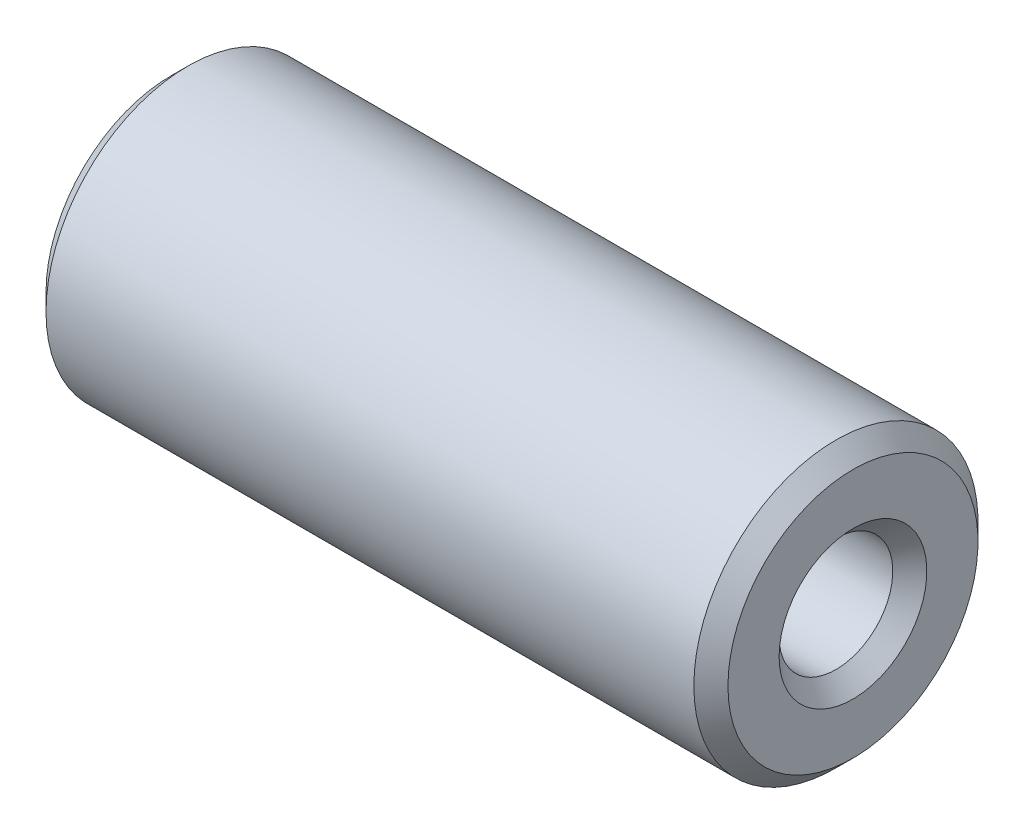
SolidWorks part; units mm, degrees
material "Bronze pour coussinet"
ref_plane "Plan1" through (0, 0, 0) normal (0, 0, 1) x (1, 0, 0)
ref_plane "Plan2" through (0, 0, 0) normal (0, 1, 0) x (1, 0, 0)
ref_plane "Plan3" through (0, 0, 0) normal (1, 0, 0) x (0, 0, -1)
sketch "Esquisse1" plane through (0, 0, 0) normal (0, 0, 1) x (1, 0, 0)
  line L0 (0, 1.3) -> (0, 2.2)
  line L1 (0, 2.2) -> (0.3, 2.5)
  line L2 (0.3, 2.5) -> (11.7, 2.5)
  line L3 (11.7, 2.5) -> (12, 2.2)
  line L4 (12, 2.2) -> (12, 1.3)
  line L5 (12, 1.3) -> (11.7, 1)
  line L6 (11.7, 1) -> (0.3, 1)
  line L7 (0.3, 1) -> (0, 1.3)
  line L8 (0, 0) -> (12, 0) construction
  dimension "D1" = 1
  dimension "D2" = 2.5
  dimension "D3" = 12
  dimension "D4" = 45
  dimension "D5" = 45
  dimension "D6" = 45
  dimension "D7" = 45
revolve "Base-Révolution" add sketch "Esquisse1" angle 360 about L8
